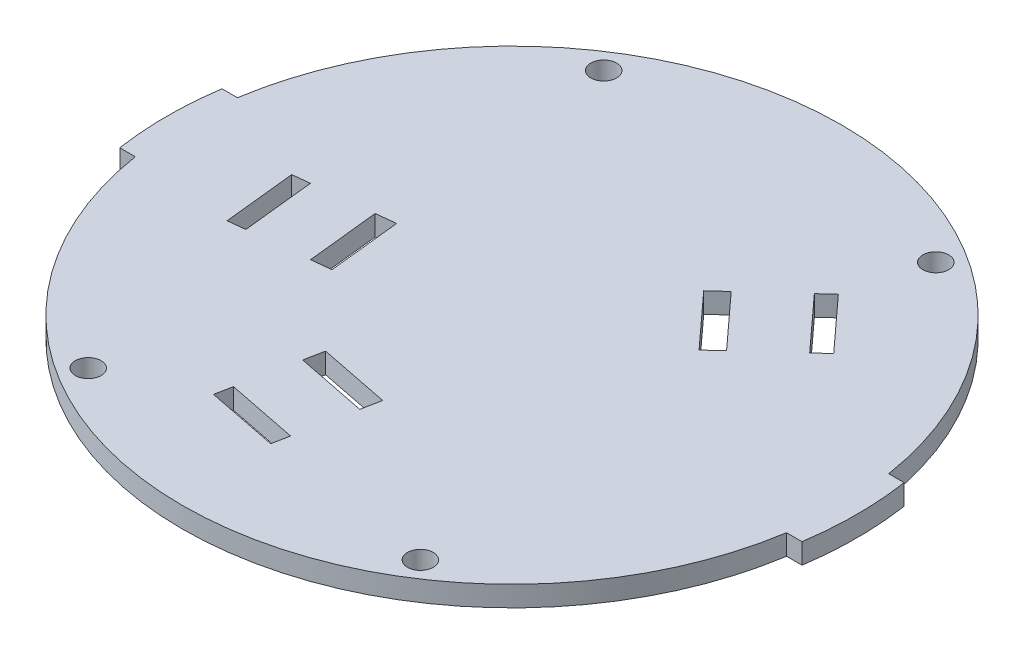
SolidWorks part; units mm, degrees
material "ABS"
ref_plane "Front Plane" through (0, 0, 0) normal (0, 0, 1) x (1, 0, 0)
ref_plane "Top Plane" through (0, 0, 0) normal (0, 1, 0) x (1, 0, 0)
ref_plane "Right Plane" through (0, 0, 0) normal (1, 0, 0) x (0, 0, -1)
sketch "Sketch1" plane through (0, 0, 0) normal (0, 1, 0) x (1, 0, 0)
  line L0 (0, 0) -> (-75.1171, 0) construction
  line L1 (-63.7201, -12.3966) -> (-66.7551, -12.3966)
  line L2 (-66.7551, 7.6034) -> (-63.7201, 7.6034)
  line L3 (0, 0) -> (0, -66.8966) construction
  line L4 (66.7551, 7.6034) -> (63.7201, 7.6034)
  line L5 (63.7201, -12.3966) -> (66.7551, -12.3966)
  arc A0 (-63.7201, -12.3966) -> (63.7201, -12.3966) centre (0, -2.3966) ccw construction
  arc A2 (-66.7551, 7.6034) -> (-66.7551, -12.3966) centre (0, -2.3966) ccw
  arc A3 (66.7551, 7.6034) -> (66.7551, -12.3966) centre (0, -2.3966) cw
  arc A7 (-63.7201, -12.3966) -> (63.7201, -12.3966) centre (0, -2.3966) ccw
  arc A8 (63.7201, 7.6034) -> (-63.7201, 7.6034) centre (0, -2.3966) ccw
extrude "Boss-Extrude1" add sketch "Sketch1" against normal blind 4
sketch "Sketch2" plane through (0, -4, 0) normal (0, -1, 0) x (1, 0, 0)
  line L0 (-32.5, 52.8322) -> (32.5, 52.8322) construction
  line L1 (32.5, 52.8322) -> (32.5, -48.039) construction
  line L2 (32.5, -48.039) -> (-32.5, -48.039) construction
  line L3 (-32.5, -48.039) -> (-32.5, 52.8322) construction
hole_wizard "#8 (0.199) Diameter Hole6" positions "3DSketch1" profile "Sketch3" hole size "#8" standard "ANSI Inch" end condition through all
sketch3d "3DSketch1"
  point P0 (-32.5, -4, 52.8322)
  point P3 (32.5, -4, 52.8322)
  point P6 (32.5, -4, -48.039)
  point P9 (-32.5, -4, -48.039)
sketch "Sketch3" plane through (-32.5, -4, 52.8322) normal (1, 0, 0) x (0, 0, -1)
  line L0 (0, 0) -> (0, 4)
  line L1 (0, 4) -> (2.5273, 4)
  line L2 (2.5273, 4) -> (2.5273, 0)
  line L5 (2.5273, 0) -> (0, 0)
  line L11 (0, -6.35) -> (0, 107.95) construction
  dimension "Thru Hole Dia." = 5.0546
  dimension "Thru Hole Depth" = 4
sketch "Sketch4" plane through (0, -4, 0) normal (0, -1, 0) x (1, 0, 0)
  line L0 (17.426, -23.0749) -> (14.6125, -20.5057)
  line L1 (14.6125, -20.5057) -> (24.2042, -10.0022)
  line L2 (24.2042, -10.0022) -> (27.0176, -12.5714)
  line L3 (27.0176, -12.5714) -> (17.426, -23.0749)
  line L4 (28.3857, -33.0833) -> (25.9294, -30.8401)
  line L5 (25.9294, -30.8401) -> (35.521, -20.3367)
  line L6 (35.521, -20.3367) -> (37.9774, -22.5798)
  line L7 (37.9774, -22.5798) -> (28.3857, -33.0833)
  line L8 (28.3857, -33.0833) -> (25.9294, -30.8401) construction
  line L9 (37.9774, -22.5798) -> (28.3857, -33.0833) construction
  line L10 (-11.8499, -18.8788) -> (-24.3499, 2.7719) construction
  line L11 (45.5648, -22.2851) -> (23.8623, -2.4666) construction
  line L12 (-49.8024, -11.9231) -> (-37.3024, -33.5738) construction
  line L14 (-26.8326, -1.852) -> (-30.6213, -1.4498)
  line L15 (-30.6213, -1.4498) -> (-29.1194, 12.6947)
  line L16 (-29.1194, 12.6947) -> (-30.6213, -1.4498) construction
  line L17 (-29.1194, 12.6947) -> (-25.3307, 12.2925) construction
  line L18 (-29.1194, 12.6947) -> (-25.3307, 12.2925)
  line L19 (-25.3307, 12.2925) -> (-26.8326, -1.852)
  line L20 (-42.0724, -0.2339) -> (-45.3803, 0.1174)
  line L21 (-45.3803, 0.1174) -> (-43.8785, 14.2618)
  line L25 (-43.8785, 14.2618) -> (-40.5706, 13.9106)
  line L26 (-40.5706, 13.9106) -> (-42.0724, -0.2339) construction
  line L27 (-40.5706, 13.9106) -> (-42.0724, -0.2339)
  line L28 (1.8012, 29.5036) -> (-12.1491, 26.7271)
  line L29 (-12.1491, 26.7271) -> (-12.8929, 30.4638)
  line L30 (-12.8929, 30.4638) -> (1.0575, 33.2403)
  line L31 (1.0575, 33.2403) -> (1.8012, 29.5036)
  line L32 (-1.1904, 44.5343) -> (-15.1407, 41.7577)
  line L37 (-15.1407, 41.7577) -> (-15.7901, 45.0202)
  line L38 (-15.7901, 45.0202) -> (-1.8397, 47.7968)
  line L39 (-1.8397, 47.7968) -> (-1.1904, 44.5343)
  dimension "D1" = 5.334
  dimension "D2" = 11.5155
  dimension "D3" = 5.334
  dimension "D4" = 5.404
sketch "Sketch5" plane through (0, 6, 0) normal (0, 1, 0) x (1, 0, 0)
  circle A0 centre (0, 0) radius 65.1034 construction
extrude "Cut-Extrude1" cut sketch "Sketch4" against normal up to surface (4 mm away) up to face at (-32.5, 0, 50.3049)
